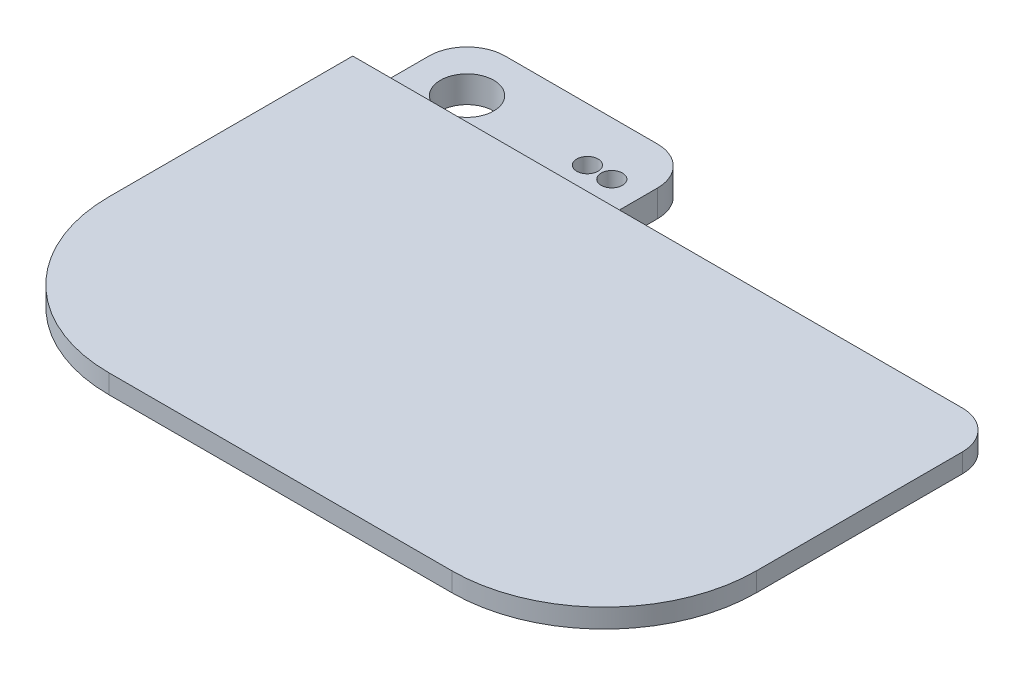
SolidWorks part; units mm, degrees
ref_plane "Front Plane" through (0, 0, 0) normal (0, 0, 1) x (1, 0, 0)
ref_plane "Top Plane" through (0, 0, 0) normal (0, 1, 0) x (1, 0, 0)
ref_plane "Right Plane" through (0, 0, 0) normal (1, 0, 0) x (0, 0, -1)
sketch "Sketch1" plane through (0, 0, 0) normal (0, 1, 0) x (1, 0, 0)
  line L1 (0, 0) -> (107.95, 0)
  line L2 (0, 0) -> (0, 85.09)
  line L3 (0, 85.09) -> (107.95, 85.09)
  line L4 (107.95, 0) -> (107.95, 85.09)
  circle A0 centre (8.89, 76.2) radius 4.445
  dimension "D5" = 8.89
  dimension "D1" = 85.09
  dimension "D2" = 107.95
  dimension "D3" = 8.89
  dimension "D4" = 8.89
extrude "Boss-Extrude1" add sketch "Sketch1" along normal blind 3.175
sketch "Sketch2" plane through (0, 0, 0) normal (0, -1, 0) x (1, 0, 0)
  line L0 (107.95, 0) -> (107.95, -85.09) construction
  line L1 (0, -85.09) -> (107.95, -85.09)
  line L2 (0, -85.09) -> (0, -59.69)
  line L3 (0, -59.69) -> (107.95, -59.69)
  line L4 (107.95, -85.09) -> (107.95, -59.69)
  circle A0 centre (8.89, -76.2) radius 4.445 construction
  circle A1 centre (8.89, -76.2) radius 4.445
  dimension "D1" = 25.4
extrude "Boss-Extrude2" add sketch "Sketch2" along normal blind 7.62
sketch "Sketch3" plane through (0, -7.62, 0) normal (0, -1, 0) x (1, 0, 0)
  line L0 (107.95, -59.69) -> (0, -59.69) construction
  line L1 (107.95, -85.09) -> (38.1, -85.09)
  line L2 (107.95, -85.09) -> (107.95, -66.04)
  line L3 (107.95, -66.04) -> (38.1, -66.04)
  line L4 (38.1, -85.09) -> (38.1, -66.04)
  line L5 (0, -59.69) -> (0, -85.09) construction
  dimension "D1" = 6.35
  dimension "D2" = 38.1
extrude "Cut-Extrude1" cut sketch "Sketch3" against normal through all
sketch "Sketch4" plane through (0, 3.175, 0) normal (0, 1, 0) x (1, 0, 0)
  line L1 (38.1, 66.04) -> (0, 66.04)
  line L2 (38.1, 66.04) -> (38.1, 85.09)
  line L3 (38.1, 85.09) -> (0, 85.09)
  line L4 (0, 66.04) -> (0, 85.09)
extrude "Cut-Extrude2" cut sketch "Sketch4" against normal blind 6.35
sketch "Sketch5" plane through (0, -3.175, 0) normal (0, 1, 0) x (1, 0, 0)
  line L0 (8.89, 76.2) -> (50008.89, 76.2) construction
  circle A0 centre (28.956, 76.2) radius 1.778
  circle A1 centre (33.02, 76.2) radius 1.778
  circle A2 centre (8.89, 76.2) radius 4.445 construction
  dimension "D1" = 3.556
  dimension "D3" = 4.064
  dimension "D2" = 20.066
extrude "Cut-Extrude3" cut sketch "Sketch5" against normal through all
sketch "Sketch6" plane through (0, 0, -59.69) normal (0, 0, 1) x (1, 0, 0)
  line L0 (107.95, -7.62) -> (0, -7.62) construction
  line L1 (107.95, 0) -> (88.9, 0)
  line L2 (107.95, 0) -> (107.95, -7.62)
  line L3 (107.95, -7.62) -> (88.9, -7.62)
  line L4 (88.9, 0) -> (88.9, -7.62)
  dimension "D1" = 19.05
extrude "Cut-Extrude4" cut sketch "Sketch6" against normal through all
sketch "Sketch7" plane through (0, 0, 0) normal (-1, 0, 0) x (0, 0, 1)
  line L0 (-66.04, 3.175) -> (-71.12, -3.175)
  line L1 (-85.09, -3.175) -> (-66.04, -3.175) construction
  line L2 (-71.12, -3.175) -> (-66.04, -3.175)
  line L3 (-66.04, -3.175) -> (-66.04, 3.175)
  dimension "D1" = 5.08
extrude "Boss-Extrude3" add sketch "Sketch7" against normal up to surface (38.1 mm away) up to face at (38.1, -5.3975, -75.565)
fillet "Fillet1" radius 25.4 2 edges at (107.95, 1.5875, 0) (0, 1.5875, 0)
fillet "Fillet2" radius 6.35 3 edges at (107.95, 1.5875, -66.04) (0, -5.3975, -85.09) (38.1, -5.3975, -85.09)
fillet "Fillet3" radius 3.175 2 edges at (88.9, 0, -62.865) (88.9, -7.62, -62.865)
